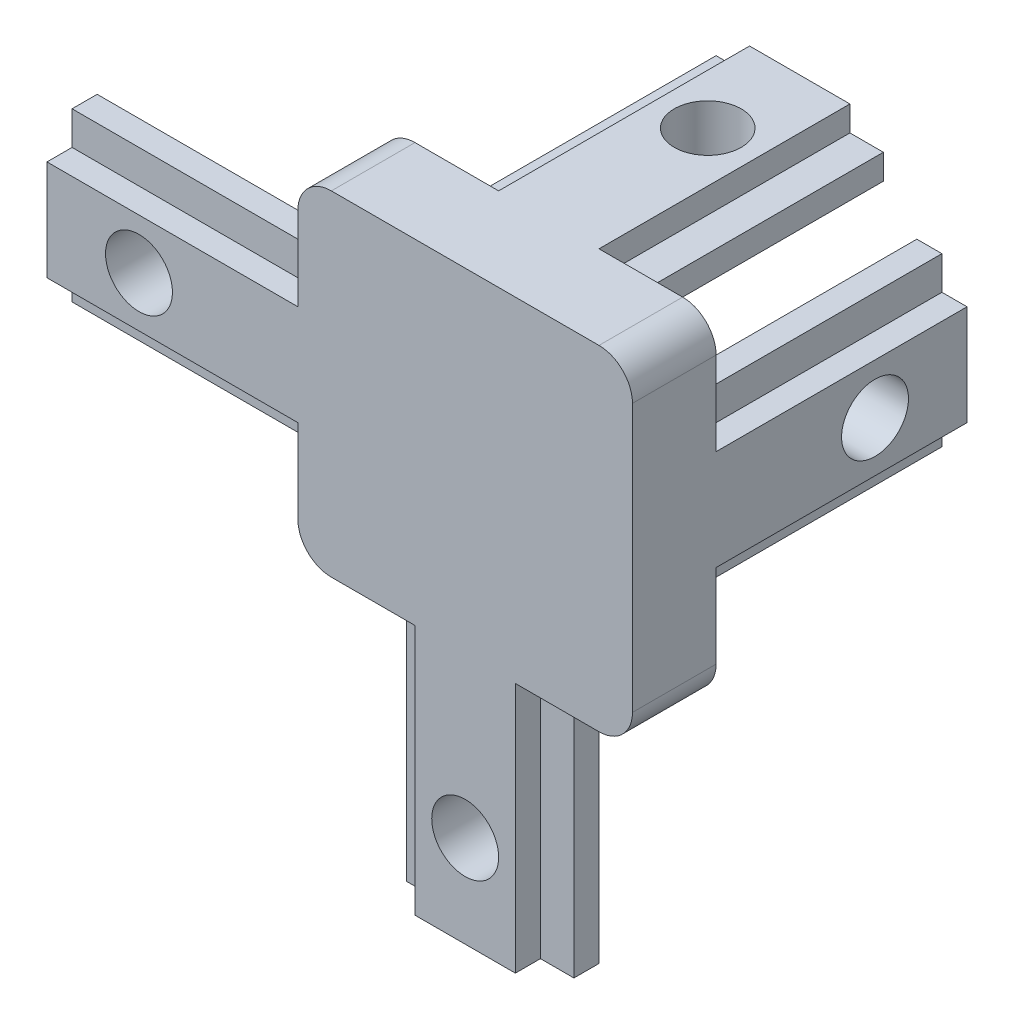
SolidWorks part; units mm, degrees
ref_plane "Front Plane" through (0, 0, 0) normal (0, 0, 1) x (1, 0, 0)
ref_plane "Top Plane" through (0, 0, 0) normal (0, 1, 0) x (1, 0, 0)
ref_plane "Right Plane" through (0, 0, 0) normal (1, 0, 0) x (0, 0, -1)
ref_plane "Plane1" through (0, 0, -5) normal (0, 0, -1) x (-1, 0, 0)
sketch "Sketch1" plane through (0, 0, -5) normal (0, 0, -1) x (-1, 0, 0)
  line L0 (-20, 5) -> (15, 5)
  line L1 (15, 5) -> (15, 15)
  line L2 (15, 15) -> (-20, 15)
  line L3 (-20, 15) -> (-20, 5)
extrude "Boss-Extrude1" add sketch "Sketch1" against normal blind 5
sketch "Sketch2" plane through (-15, 0, 0) normal (-1, 0, 0) x (0, 0, 1)
  line L0 (-3, 5) -> (-5, 7)
  line L1 (-5, 7) -> (-5, 5)
  line L2 (-5, 5) -> (-3, 5)
extrude "Cut-Extrude1" cut sketch "Sketch2" against normal blind 15
sketch "Sketch3" plane through (0, 5, 0) normal (0, -1, 0) x (1, 0, 0)
  line L0 (0, -5) -> (0, 0)
  line L1 (0, 0) -> (20, 0)
  line L2 (20, 0) -> (20, -5)
  line L3 (20, -5) -> (0, -5)
extrude "Boss-Extrude2" add sketch "Sketch3" along normal blind 5
sketch "Sketch4" plane through (-15, 0, 0) normal (-1, 0, 0) x (0, 0, 1)
  line L0 (-5, 13) -> (-3, 15)
  line L1 (-3, 15) -> (-5, 15)
  line L2 (-5, 15) -> (-5, 13)
extrude "Cut-Extrude2" cut sketch "Sketch4" against normal blind 15
sketch "Sketch5" plane through (0, 15, 0) normal (0, 1, 0) x (-1, 0, 0)
  line L0 (-20, -5) -> (-20, 0)
  line L1 (-20, 0) -> (0, 0)
  line L2 (0, 0) -> (0, -5)
  line L3 (0, -5) -> (-20, -5)
extrude "Boss-Extrude3" add sketch "Sketch5" along normal blind 5
sketch "Sketch6" plane through (0, 0, 0) normal (0, -1, 0) x (1, 0, 0)
  line L0 (15, 0) -> (15, -3)
  line L1 (15, -3) -> (13, -5)
  line L2 (13, -5) -> (7, -5)
  line L3 (7, -5) -> (5, -3)
  line L4 (5, -3) -> (5, 0)
  line L5 (5, 0) -> (15, 0)
extrude "Boss-Extrude4" add sketch "Sketch6" along normal blind 15
sketch "Sketch7" plane through (0, 0, -5) normal (0, 0, -1) x (-1, 0, 0)
  line L0 (-5, 20) -> (-5, 17)
  line L1 (-5, 17) -> (-7, 15)
  line L2 (-7, 15) -> (-13, 15)
  line L3 (-13, 15) -> (-15, 17)
  line L4 (-15, 17) -> (-15, 20)
  line L5 (-15, 20) -> (-5, 20)
extrude "Boss-Extrude5" add sketch "Sketch7" along normal blind 15
sketch "Sketch8" plane through (0, 0, -5) normal (0, 0, -1) x (-1, 0, 0)
  line L0 (-20, 5) -> (-20, 15)
  line L1 (-20, 15) -> (-17, 15)
  line L2 (-17, 15) -> (-15, 13)
  line L3 (-15, 13) -> (-15, 7)
  line L4 (-15, 7) -> (-17, 5)
  line L5 (-17, 5) -> (-20, 5)
extrude "Boss-Extrude6" add sketch "Sketch8" along normal blind 15
sketch "Sketch9" plane through (0, 0, -5) normal (0, 0, -1) x (-1, 0, 0)
  line L0 (-16, 16) -> (-16, 14)
  line L1 (-16, 14) -> (-15, 13)
  line L2 (-15, 13) -> (-15, 7)
  line L3 (-15, 7) -> (-16, 6)
  line L4 (-16, 6) -> (-16, 4)
  line L5 (-16, 4) -> (-4, 4)
  line L6 (-4, 4) -> (-4, 16)
  line L7 (-4, 16) -> (-6, 16)
  line L8 (-6, 16) -> (-7, 15)
  line L9 (-7, 15) -> (-13, 15)
  line L10 (-13, 15) -> (-14, 16)
  line L11 (-14, 16) -> (-16, 16)
extrude "Cut-Extrude3" cut sketch "Sketch9" against normal blind 1
sketch "Sketch10" plane through (5, 0, 0) normal (-1, 0, 0) x (0, 0, 1)
  line L0 (-5, 18.5) -> (-5, 20)
  line L1 (-5, 20) -> (-20, 20)
  line L2 (-20, 20) -> (-20, 18.5)
  line L3 (-20, 18.5) -> (-5, 18.5)
extrude "Cut-Extrude4" cut sketch "Sketch10" against normal blind 2
sketch "Sketch11" plane through (0, -15, 0) normal (0, -1, 0) x (1, 0, 0)
  line L0 (5, -1.5) -> (7, -1.5)
  line L1 (7, -1.5) -> (7, 0)
  line L2 (7, 0) -> (5, 0)
  line L3 (5, 0) -> (5, -1.5)
extrude "Cut-Extrude5" cut sketch "Sketch11" against normal blind 15
sketch "Sketch12" plane through (-15, 0, 0) normal (-1, 0, 0) x (0, 0, 1)
  line L0 (-1.5, 15) -> (-1.5, 13)
  line L1 (-1.5, 13) -> (0, 13)
  line L2 (0, 13) -> (0, 15)
  line L3 (0, 15) -> (-1.5, 15)
extrude "Cut-Extrude6" cut sketch "Sketch12" against normal blind 15
sketch "Sketch13" plane through (-15, 0, 0) normal (-1, 0, 0) x (0, 0, 1)
  line L0 (0, 5) -> (0, 7)
  line L1 (0, 7) -> (-1.5, 7)
  line L2 (-1.5, 7) -> (-1.5, 5)
  line L3 (-1.5, 5) -> (0, 5)
extrude "Cut-Extrude7" cut sketch "Sketch13" against normal blind 15
sketch "Sketch14" plane through (0, -15, 0) normal (0, -1, 0) x (1, 0, 0)
  line L0 (15, 0) -> (13, 0)
  line L1 (13, 0) -> (13, -1.5)
  line L2 (13, -1.5) -> (15, -1.5)
  line L3 (15, -1.5) -> (15, 0)
extrude "Cut-Extrude8" cut sketch "Sketch14" against normal blind 15
sketch "Sketch15" plane through (0, 5, 0) normal (0, -1, 0) x (1, 0, 0)
  line L0 (20, -5) -> (18.5, -5)
  line L1 (18.5, -5) -> (18.5, -20)
  line L2 (18.5, -20) -> (20, -20)
  line L3 (20, -20) -> (20, -5)
extrude "Cut-Extrude9" cut sketch "Sketch15" against normal blind 2
sketch "Sketch16" plane through (0, 15, 0) normal (0, 1, 0) x (-1, 0, 0)
  line L0 (-18.5, -5) -> (-20, -5)
  line L1 (-20, -5) -> (-20, -20)
  line L2 (-20, -20) -> (-18.5, -20)
  line L3 (-18.5, -20) -> (-18.5, -5)
extrude "Cut-Extrude10" cut sketch "Sketch16" against normal blind 2
sketch "Sketch17" plane through (0, 0, -20) normal (0, 0, -1) x (-1, 0, 0)
  line L0 (-15, 18.5) -> (-13, 18.5)
  line L1 (-13, 18.5) -> (-13, 20)
  line L2 (-13, 20) -> (-15, 20)
  line L3 (-15, 20) -> (-15, 18.5)
extrude "Cut-Extrude11" cut sketch "Sketch17" against normal blind 15
hole_wizard "#6 Clearance Hole1" positions "Sketch19" profile "Sketch18" hole size "#6" standard "ANSI Inch"
sketch "Sketch19" plane through (0, 0, -5) normal (0, 0, -1) x (-1, 0, 0)
  point P0 (-10, -9.5)
  point P1 (9.5, 10)
sketch "Sketch18" plane through (10, -9.5, -5) normal (1, 0, 0) x (0, 1, 0)
  line L0 (0, 0) -> (0, 5)
  line L1 (0, 5) -> (2, 5)
  line L2 (2, 5) -> (2, 0)
  line L5 (2, 0) -> (0, 0)
  line L11 (0, -6.35) -> (0, 107.95) construction
  dimension "Thru Hole Dia." = 4
  dimension "Thru Hole Depth" = 5
hole_wizard "#6 Clearance Hole2" positions "Sketch21" profile "Sketch20" hole size "#6" standard "ANSI Inch"
sketch "Sketch21" plane through (0, 20, 0) normal (0, 1, 0) x (1, 0, 0)
  point P0 (10, 14.5)
sketch "Sketch20" plane through (10, 20, -14.5) normal (1, 0, 0) x (0, 0, 1)
  line L0 (0, 0) -> (0, 35)
  line L1 (0, 35) -> (2, 35)
  line L2 (2, 35) -> (2, 0)
  line L5 (2, 0) -> (0, 0)
  line L11 (0, -6.35) -> (0, 107.95) construction
  dimension "Thru Hole Dia." = 4
  dimension "Thru Hole Depth" = 35
hole_wizard "#6 Clearance Hole3" positions "Sketch23" profile "Sketch22" hole size "#6" standard "ANSI Inch"
sketch "Sketch23" plane through (20, 0, 0) normal (1, 0, 0) x (0, 0, -1)
  point P0 (14.5, 10)
sketch "Sketch22" plane through (20, 10, -14.5) normal (0, 1, 0) x (0, 0, -1)
  line L0 (0, 0) -> (0, 35)
  line L1 (0, 35) -> (2, 35)
  line L2 (2, 35) -> (2, 0)
  line L5 (2, 0) -> (0, 0)
  line L11 (0, -6.35) -> (0, 107.95) construction
  dimension "Thru Hole Dia." = 4
  dimension "Thru Hole Depth" = 35
fillet "Fillet1" radius 2 4 edges at (0, 0, -2.5) (0, 20, -2.5) (20, 20, -2.5) (20, 0, -2.5)
